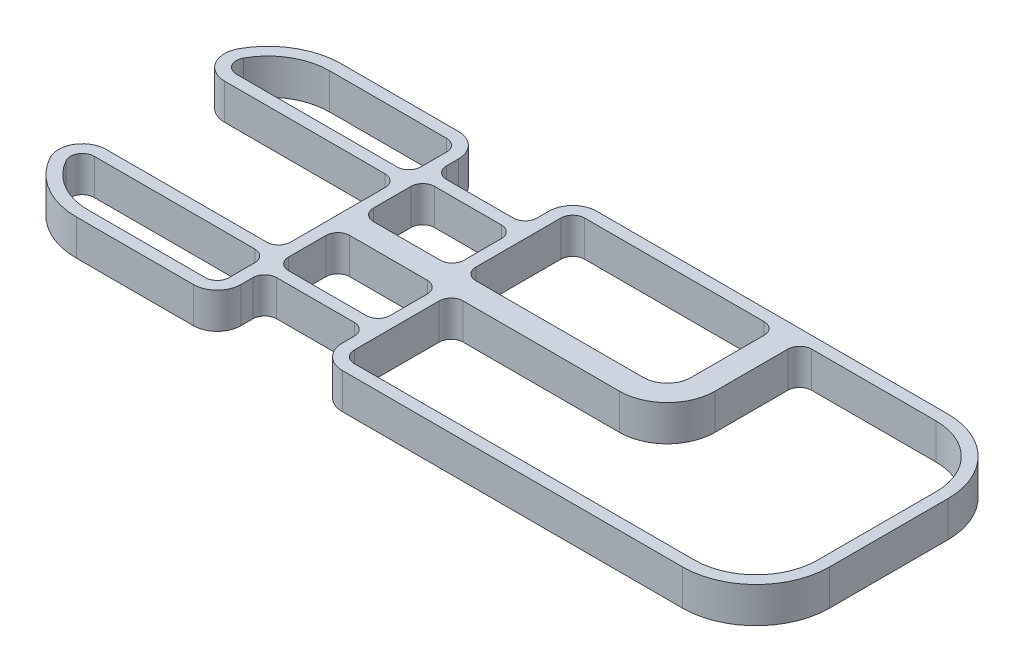
SolidWorks part; units mm, degrees
ref_plane "Front Plane" through (0, 0, 0) normal (0, 0, 1) x (1, 0, 0)
ref_plane "Top Plane" through (0, 0, 0) normal (0, 1, 0) x (1, 0, 0)
ref_plane "Right Plane" through (0, 0, 0) normal (1, 0, 0) x (0, 0, -1)
sketch "Sketch1" plane through (0, 0, 0) normal (0, 1, 0) x (1, 0, 0)
  line L0 (127.1844, 54.2784) -> (127.1844, 3.4784) construction
  line L1 (215.8621, 1.351) -> (-215.9379, 1.351) construction
  line L2 (-200.9203, 32.917) -> (-200.9203, -30.2149)
  line L3 (-161.7789, -69.3563) -> (-86.6203, -69.3563)
  line L4 (200.8444, -30.2149) -> (200.8444, 32.917)
  line L5 (161.703, 72.0584) -> (-38.3603, 72.0584)
  line L6 (161.703, 65.7084) -> (-38.3603, 65.7084)
  line L7 (-194.5703, 32.917) -> (-194.5703, -30.2149)
  line L8 (-161.7789, -63.0063) -> (-86.6203, -63.0063)
  line L9 (194.4944, -30.2149) -> (194.4944, 32.917)
  line L10 (-86.6203, 72.0584) -> (-86.6203, 65.7084)
  line L11 (-38.3603, 72.0584) -> (-38.3603, 65.7084)
  line L12 (-86.6203, -63.0063) -> (-86.6203, -69.3563)
  line L13 (-32.5183, -63.0063) -> (-32.5183, -69.3563)
  line L14 (-86.6203, 65.7084) -> (-161.7789, 65.7084)
  line L15 (161.703, 65.7084) -> (-161.7789, 65.7084) construction
  line L16 (-86.6203, 72.0584) -> (-161.7789, 72.0584)
  line L17 (161.703, 72.0584) -> (-161.7789, 72.0584) construction
  line L18 (-32.5183, -63.0063) -> (161.703, -63.0063)
  line L19 (-161.7789, -63.0063) -> (161.703, -63.0063) construction
  line L20 (-32.5183, -69.3563) -> (161.703, -69.3563)
  line L21 (-161.7789, -69.3563) -> (161.703, -69.3563) construction
  circle A0 centre (-112.0203, -1.6016) radius 3.15 construction
  circle A1 centre (-137.4203, -1.6016) radius 3.15 construction
  circle A2 centre (-162.8203, -1.6016) radius 3.15 construction
  circle A3 centre (-188.2203, -1.6016) radius 5.7544 construction
  circle A4 centre (-137.4203, 23.7984) radius 3.15 construction
  circle A5 centre (-162.8203, 23.7984) radius 3.15 construction
  circle A6 centre (-188.2203, 23.7984) radius 3.15 construction
  circle A7 centre (-45.2183, -56.6563) radius 5.7544 construction
  circle A8 centre (-73.9203, -56.6563) radius 5.7544 construction
  circle A9 centre (-73.9203, 59.3584) radius 5.7544 construction
  circle A10 centre (-51.0603, 59.3584) radius 5.7544 construction
  circle A11 centre (99.2444, -20.3343) radius 5.7544 construction
  circle A12 centre (70.5424, -20.3343) radius 5.7544 construction
  circle A13 centre (41.8404, -20.3343) radius 5.7544 construction
  circle A14 centre (13.1384, -20.3343) radius 5.7544 construction
  circle A15 centre (99.2444, -49.0363) radius 5.7544 construction
  circle A16 centre (70.5424, -49.0363) radius 5.7544 construction
  circle A17 centre (41.8404, -49.0363) radius 5.7544 construction
  circle A18 centre (13.1384, -49.0363) radius 5.7544 construction
  circle A19 centre (127.1844, 54.2784) radius 5.0991 construction
  circle A20 centre (127.1844, 3.4784) radius 5.7544 construction
  circle A21 centre (45.2694, 55.5484) radius 5.7544 construction
  circle A22 centre (45.2694, 26.9734) radius 3.15 construction
  circle A23 centre (16.6944, 26.9734) radius 3.15 construction
  circle A24 centre (16.6944, 55.5484) radius 5.7544 construction
  circle A25 centre (-11.8806, 55.5484) radius 5.7544 construction
  circle A26 centre (165.2844, 28.8784) radius 12.954 construction
  circle A27 centre (-11.8806, 26.9734) radius 5.7544 construction
  circle A28 centre (165.2844, -25.9856) radius 12.954 construction
  arc A29 (-161.7789, 72.0584) -> (-200.9203, 32.917) centre (-161.7789, 32.917) ccw
  arc A30 (-200.9203, -30.2149) -> (-161.7789, -69.3563) centre (-161.7789, -30.2149) ccw
  arc A31 (161.703, -69.3563) -> (200.8444, -30.2149) centre (161.703, -30.2149) ccw
  arc A32 (200.8444, 32.917) -> (161.703, 72.0584) centre (161.703, 32.917) ccw
  arc A33 (-161.7789, 65.7084) -> (-194.5703, 32.917) centre (-161.7789, 32.917) ccw
  arc A34 (-194.5703, -30.2149) -> (-161.7789, -63.0063) centre (-161.7789, -30.2149) ccw
  arc A35 (161.703, -63.0063) -> (194.4944, -30.2149) centre (161.703, -30.2149) ccw
  arc A36 (194.4944, 32.917) -> (161.703, 65.7084) centre (161.703, 32.917) ccw
  point P0 (-11.8806, 26.9734)
  point P13 (127.1844, 28.8784)
  point P76 (-200.9203, 1.351)
  point P77 (200.8444, 1.351)
  dimension "D3" = 39.1414
  dimension "D1" = 141.4147
  dimension "D2" = 401.7647
  dimension "D4" = 90
  dimension "D5" = 12.7
  dimension "D7" = 12.7
  dimension "D8" = 12.7
  dimension "D9" = 12.7
  dimension "D10" = 12.7
  dimension "D6" = 6.35
extrude "Boss-Extrude1" add sketch "Sketch1" along normal blind 19.05
sketch "Sketch4" plane through (0, 19.05, 0) normal (0, 1, 0) x (1, 0, 0)
  line L1 (-200.9203, 32.917) -> (-194.5703, 32.917)
  line L2 (-200.9203, 32.917) -> (-200.9203, -30.2149)
  line L3 (-200.9203, -30.2149) -> (-194.5703, -30.2149)
  line L4 (-194.5703, 32.917) -> (-194.5703, -30.2149)
extrude "Cut-Extrude4" cut sketch "Sketch4" against normal blind 19.05
sketch "Sketch5" plane through (0, 0, 0) normal (0, 1, 0) x (1, 0, 0)
  line L0 (-194.5703, -30.2149) -> (-86.6203, -30.2149)
  line L1 (-86.6203, -30.2149) -> (-86.6203, -63.0063)
  line L2 (-193.9496, -36.5649) -> (-92.9703, -36.5649)
  line L3 (-92.9703, -36.5649) -> (-92.9703, -63.0063)
  line L4 (-161.7789, -63.0063) -> (-86.6203, -63.0063) construction
  line L5 (-92.9703, -63.0063) -> (-86.6203, -63.0063)
  line L6 (-194.5703, -36.5649) -> (-92.9703, -36.5649) construction
  line L7 (215.8621, 1.351) -> (-215.9379, 1.351) construction
  line L8 (215.8621, 1.351) -> (-215.9379, 1.351) construction
  line L9 (-92.9703, 65.7084) -> (-86.6203, 65.7084)
  line L10 (-92.9703, 39.267) -> (-92.9703, 65.7084)
  line L11 (-193.9496, 39.267) -> (-92.9703, 39.267)
  line L12 (-86.6203, 32.917) -> (-86.6203, 65.7084)
  line L13 (-194.5703, 32.917) -> (-86.6203, 32.917)
  arc A0 (-194.5703, -30.2149) -> (-161.7789, -63.0063) centre (-161.7789, -30.2149) ccw construction
  arc A1 (-194.5703, -30.2149) -> (-193.9496, -36.5649) centre (-161.7789, -30.2149) ccw
  arc A2 (-194.5703, 32.917) -> (-193.9496, 39.267) centre (-161.7789, 32.917) cw
  dimension "D1" = 6.35
extrude "Boss-Extrude2" add sketch "Sketch5" along normal blind 19.05
sketch "Sketch6" plane through (0, 0, 0) normal (0, 1, 0) x (1, 0, 0)
  line L0 (-86.6203, -43.9563) -> (-32.5183, -43.9563)
  line L1 (-86.6203, -69.3563) -> (-86.6203, -30.2149) construction
  line L2 (-32.5183, -43.9563) -> (-32.5183, -63.0063)
  line L3 (-86.6203, -37.6063) -> (-32.5183, -37.6063)
  line L4 (-26.1683, -37.6063) -> (-26.1683, -63.0063)
  line L5 (-32.5183, -63.0063) -> (161.703, -63.0063) construction
  line L6 (-86.6203, -43.9563) -> (-86.6203, -37.6063)
  line L7 (-32.5183, -63.0063) -> (-26.1683, -63.0063)
  line L8 (-38.3603, 65.7084) -> (-38.3603, 46.6584)
  line L9 (-38.3603, 46.6584) -> (-86.6203, 46.6584)
  line L10 (-86.6203, 32.917) -> (-86.6203, 72.0584) construction
  line L11 (-32.0103, 65.7084) -> (-32.0103, 40.3084)
  line L12 (161.703, 65.7084) -> (-38.3603, 65.7084) construction
  line L13 (-38.3603, 40.3084) -> (-86.6203, 40.3084)
  line L14 (-86.6203, 40.3084) -> (-86.6203, 46.6584)
  line L15 (-38.3603, 65.7084) -> (-32.0103, 65.7084)
  line L16 (215.8621, 1.351) -> (-215.9379, 1.351) construction
  line L17 (215.8621, 1.351) -> (-215.9379, 1.351) construction
  line L18 (-92.9703, 7.701) -> (-92.9703, 32.917)
  line L19 (-86.6203, 7.701) -> (-38.3603, 7.701)
  line L20 (-92.9703, 7.701) -> (-92.9703, -4.999)
  line L21 (-86.6203, -4.999) -> (-32.5183, -4.999)
  line L23 (-86.6203, 32.917) -> (-200.9203, 32.917) construction
  line L24 (-92.9703, 32.917) -> (-86.6203, 32.917)
  line L25 (-86.6203, 32.917) -> (-86.6203, 7.701)
  line L26 (-92.9703, -4.999) -> (-92.9703, -30.2149)
  line L27 (-200.9203, -30.2149) -> (-86.6203, -30.2149) construction
  line L28 (-92.9703, -30.2149) -> (-86.6203, -30.2149)
  line L29 (-86.6203, -30.2149) -> (-86.6203, -4.999)
  line L31 (89.0844, 65.7084) -> (76.3844, 65.7084)
  line L32 (76.3844, 65.7084) -> (76.3844, 7.701)
  line L33 (89.0844, -4.999) -> (89.0844, 65.7084)
  line L34 (-26.1683, -37.6063) -> (-26.1683, -4.999)
  line L35 (-32.5183, -37.6063) -> (-32.5183, -4.999)
  line L36 (-32.0103, 40.3084) -> (-32.0103, 7.701)
  line L37 (-38.3603, 40.3084) -> (-38.3603, 7.701)
  line L38 (-32.0103, 7.701) -> (76.3844, 7.701)
  line L39 (-26.1683, -4.999) -> (89.0844, -4.999)
  point P30 (-92.9703, 1.351)
  point P45 (0, 0)
  point P52 (0, 0)
  point P54 (0, 0)
  point P55 (0, 0)
  point P56 (0, 0)
  dimension "D1" = 6.35
  dimension "D2" = 6.35
  dimension "D3" = 12.7
  dimension "D4" = 6.35
  dimension "D5" = 6.35
  dimension "D6" = 12.7
  dimension "D7" = 12.7
  dimension "D8" = 6.35
  dimension "D9" = 38.1
  dimension "D10" = 12.7
extrude "Boss-Extrude3" add sketch "Sketch6" along normal blind 19.05
fillet "Fillet2" radius 6.35 26 edges at (-38.3603, 9.525, -40.3084) (76.3844, 9.525, -65.7084) (-92.9703, 9.525, -32.917) (-86.6203, 9.525, -7.701) (-86.6203, 9.525, 4.999) (-38.3603, 9.525, -7.701) (-32.5183, 9.525, 4.999) (-32.0103, 9.525, -65.7084) (-32.0103, 9.525, -7.701) (-26.1683, 9.525, 4.999) (-38.3603, 9.525, -46.6584) (-86.6203, 9.525, -46.6584) (-86.6203, 9.525, -40.3084) (-26.1683, 9.525, 63.0063) (-32.5183, 9.525, 37.6063) (-32.5183, 9.525, 43.9563) (-86.6203, 9.525, 43.9563) (-86.6203, 9.525, 37.6063) (-92.9703, 9.525, 30.2149) (-92.9703, 9.525, -39.267) (-193.9496, 9.525, -39.267) (-92.9703, 9.525, -65.7084) (-92.9703, 9.525, 63.0063) (-193.9496, 9.525, 36.5649) (-92.9703, 9.525, 36.5649) (89.0844, 9.525, -65.7084)
fillet "Fillet3" radius 12.7 6 edges at (-38.3603, 9.525, -72.0584) (-86.6203, 9.525, -72.0584) (-200.9203, 9.525, -32.917) (-200.9203, 9.525, 30.2149) (-32.5183, 9.525, 69.3563) (-86.6203, 9.525, 69.3563)
fillet "Fillet4" radius 12.7 1 edges at (76.3844, 9.525, -7.701)
fillet "Fillet5" radius 25.4 1 edges at (89.0844, 9.525, 4.999)
